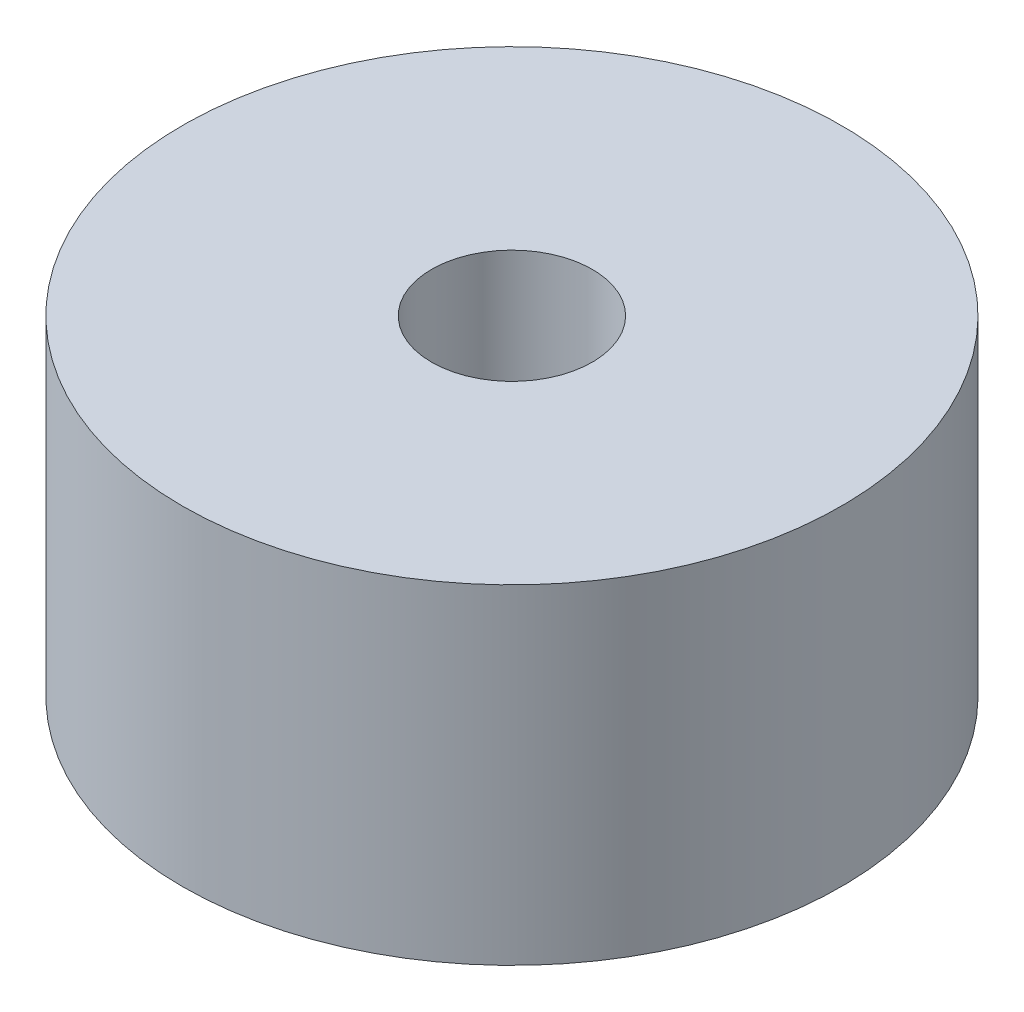
SolidWorks part; units mm, degrees
ref_plane "Front" through (0, 0, 0) normal (0, 0, 1) x (1, 0, 0)
ref_plane "Top" through (0, 0, 0) normal (0, 1, 0) x (1, 0, 0)
ref_plane "Right" through (0, 0, 0) normal (1, 0, 0) x (0, 0, -1)
sketch "Sketch1" plane through (0, 0, 0) normal (0, 1, 0) x (1, 0, 0)
  circle A0 centre (0, 0) radius 6.35
  circle A1 centre (0, 0) radius 1.5494
  dimension "D1" = 12.7
  dimension "D2" = 3.0988
extrude "Boss-Extrude1" add sketch "Sketch1" along normal blind 6.35
